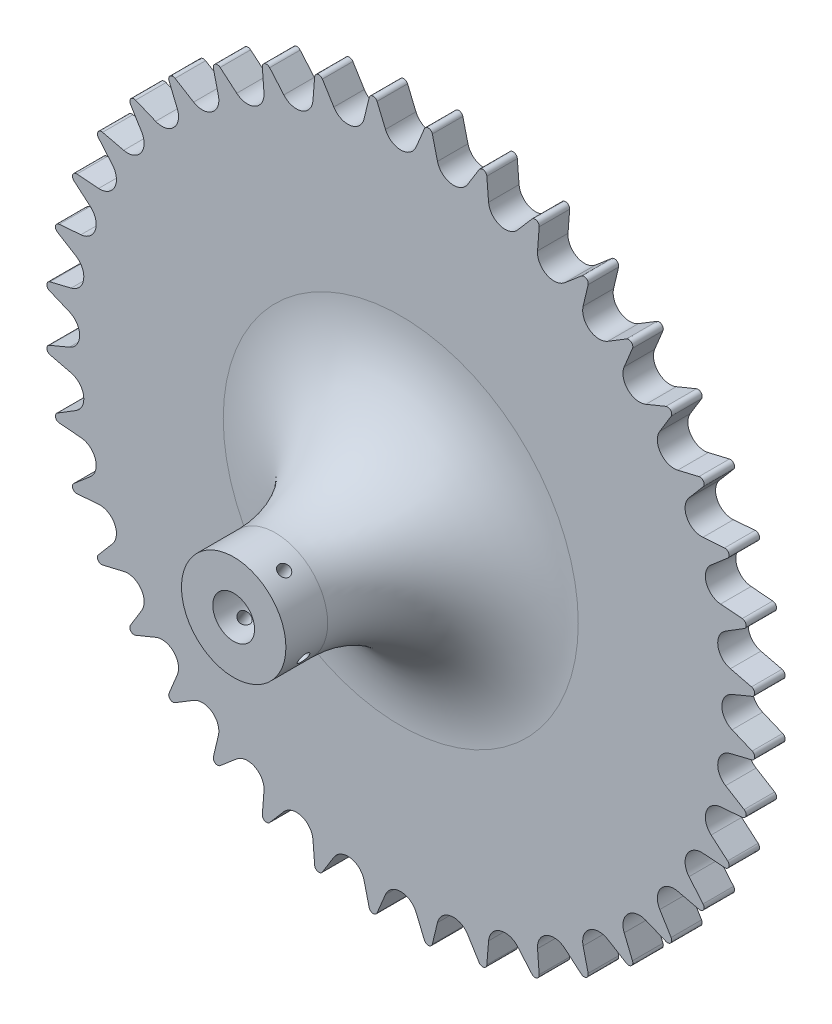
SolidWorks part; units mm, degrees
material "AISI 1010 Steel, hot rolled bar"
ref_plane "Front Plane" through (0, 0, 0) normal (0, 0, 1) x (1, 0, 0)
ref_plane "Top Plane" through (0, 0, 0) normal (0, 1, 0) x (1, 0, 0)
ref_plane "Right Plane" through (0, 0, 0) normal (1, 0, 0) x (0, 0, -1)
sketch "Sketch1" plane through (0, 0, 0) normal (0, 0, 1) x (1, 0, 0)
  line L0 (3.6626, 79.3215) -> (5.6677, 84.1262)
  line L1 (3.6626, 79.3215) -> (8.7911, 78.9179) construction
  line L2 (7.5623, 83.9771) -> (8.7911, 78.9179)
  line L3 (3.6626, 79.3215) -> (0, 0) construction
  line L4 (0, 0) -> (8.7911, 78.9179) construction
  line L5 (16.0261, 77.772) -> (18.7582, 82.2038)
  line L6 (20.6061, 81.7602) -> (21.0283, 76.5711)
  line L7 (27.995, 74.3074) -> (31.3867, 78.2573)
  line L8 (33.1425, 77.5301) -> (32.7478, 72.3388)
  line L9 (39.2746, 69.0132) -> (43.2424, 72.3839)
  line L10 (44.8629, 71.3909) -> (43.6609, 66.3253)
  line L11 (49.5871, 62.0196) -> (54.0334, 64.7281)
  line L12 (55.4785, 63.4939) -> (53.4989, 58.6786)
  line L13 (58.6786, 53.4989) -> (63.4939, 55.4785)
  line L14 (64.7281, 54.0334) -> (62.0196, 49.5871)
  line L15 (66.3253, 43.6609) -> (71.3909, 44.8629)
  line L16 (72.3839, 43.2424) -> (69.0132, 39.2746)
  line L17 (72.3388, 32.7478) -> (77.5301, 33.1425)
  line L18 (78.2573, 31.3867) -> (74.3074, 27.995)
  line L19 (76.5711, 21.0283) -> (81.7602, 20.6061)
  line L20 (82.2038, 18.7582) -> (77.772, 16.0261)
  line L21 (78.9179, 8.7911) -> (83.9771, 7.5623)
  line L22 (84.1262, 5.6677) -> (79.3215, 3.6626)
  line L23 (79.3215, -3.6626) -> (84.1262, -5.6677)
  line L24 (83.9771, -7.5623) -> (78.9179, -8.7911)
  line L25 (77.772, -16.0261) -> (82.2038, -18.7582)
  line L26 (81.7602, -20.6061) -> (76.5711, -21.0283)
  line L27 (74.3074, -27.995) -> (78.2573, -31.3867)
  line L28 (77.5301, -33.1425) -> (72.3388, -32.7478)
  line L29 (69.0132, -39.2746) -> (72.3839, -43.2424)
  line L30 (71.3909, -44.8629) -> (66.3253, -43.6609)
  line L31 (62.0196, -49.5871) -> (64.7281, -54.0334)
  line L32 (63.4939, -55.4785) -> (58.6786, -53.4989)
  line L33 (53.4989, -58.6786) -> (55.4785, -63.4939)
  line L34 (54.0334, -64.7281) -> (49.5871, -62.0196)
  line L35 (43.6609, -66.3253) -> (44.8629, -71.3909)
  line L36 (43.2424, -72.3839) -> (39.2746, -69.0132)
  line L37 (32.7478, -72.3388) -> (33.1425, -77.5301)
  line L38 (31.3867, -78.2573) -> (27.995, -74.3074)
  line L39 (21.0283, -76.5711) -> (20.6061, -81.7602)
  line L40 (18.7582, -82.2038) -> (16.0261, -77.772)
  line L41 (8.7911, -78.9179) -> (7.5623, -83.9771)
  line L42 (5.6677, -84.1262) -> (3.6626, -79.3215)
  line L43 (-3.6626, -79.3215) -> (-5.6677, -84.1262)
  line L44 (-7.5623, -83.9771) -> (-8.7911, -78.9179)
  line L45 (-16.0261, -77.772) -> (-18.7582, -82.2038)
  line L46 (-20.6061, -81.7602) -> (-21.0283, -76.5711)
  line L47 (-27.995, -74.3074) -> (-31.3867, -78.2573)
  line L48 (-33.1425, -77.5301) -> (-32.7478, -72.3388)
  line L49 (-39.2746, -69.0132) -> (-43.2424, -72.3839)
  line L50 (-44.8629, -71.3909) -> (-43.6609, -66.3253)
  line L51 (-49.5871, -62.0196) -> (-54.0334, -64.7281)
  line L52 (-55.4785, -63.4939) -> (-53.4989, -58.6786)
  line L53 (-58.6786, -53.4989) -> (-63.4939, -55.4785)
  line L54 (-64.7281, -54.0334) -> (-62.0196, -49.5871)
  line L55 (-66.3253, -43.6609) -> (-71.3909, -44.8629)
  line L56 (-72.3839, -43.2424) -> (-69.0132, -39.2746)
  line L57 (-72.3388, -32.7478) -> (-77.5301, -33.1425)
  line L58 (-78.2573, -31.3867) -> (-74.3074, -27.995)
  line L59 (-76.5711, -21.0283) -> (-81.7602, -20.6061)
  line L60 (-82.2038, -18.7582) -> (-77.772, -16.0261)
  line L61 (-78.9179, -8.7911) -> (-83.9771, -7.5623)
  line L62 (-84.1262, -5.6677) -> (-79.3215, -3.6626)
  line L63 (-79.3215, 3.6626) -> (-84.1262, 5.6677)
  line L64 (-83.9771, 7.5623) -> (-78.9179, 8.7911)
  line L65 (-77.772, 16.0261) -> (-82.2038, 18.7582)
  line L66 (-81.7602, 20.6061) -> (-76.5711, 21.0283)
  line L67 (-74.3074, 27.995) -> (-78.2573, 31.3867)
  line L68 (-77.5301, 33.1425) -> (-72.3388, 32.7478)
  line L69 (-69.0132, 39.2746) -> (-72.3839, 43.2424)
  line L70 (-71.3909, 44.8629) -> (-66.3253, 43.6609)
  line L71 (-62.0196, 49.5871) -> (-64.7281, 54.0334)
  line L72 (-63.4939, 55.4785) -> (-58.6786, 53.4989)
  line L73 (-53.4989, 58.6786) -> (-55.4785, 63.4939)
  line L74 (-54.0334, 64.7281) -> (-49.5871, 62.0196)
  line L75 (-43.6609, 66.3253) -> (-44.8629, 71.3909)
  line L76 (-43.2424, 72.3839) -> (-39.2746, 69.0132)
  line L77 (-32.7478, 72.3388) -> (-33.1425, 77.5301)
  line L78 (-31.3867, 78.2573) -> (-27.995, 74.3074)
  line L79 (-21.0283, 76.5711) -> (-20.6061, 81.7602)
  line L80 (-18.7582, 82.2038) -> (-16.0261, 77.772)
  line L81 (-8.7911, 78.9179) -> (-7.5623, 83.9771)
  line L82 (-5.6677, 84.1262) -> (-3.6626, 79.3215)
  line L83 (0, 80.85) -> (0, 0) construction
  line L84 (0, 0) -> (6.5906, 83.7411) construction
  circle A0 centre (0, 0) radius 80.85 construction
  arc A1 (-3.9676, 80.7526) -> (3.6626, 79.3215) centre (0, 80.85) ccw
  arc A2 (4.2537, 80.738) -> (8.4288, 80.4094) centre (0, 0) cw
  arc A3 (5.6677, 84.1262) -> (7.5623, 83.9771) centre (6.5906, 83.7411) cw
  arc A4 (8.7138, 80.3791) -> (16.0261, 77.772) centre (12.6477, 79.8546) ccw
  arc A5 (18.7582, 82.2038) -> (20.6061, 81.7602) centre (19.6094, 81.6791) cw
  arc A6 (21.1806, 78.0263) -> (27.995, 74.3074) centre (24.984, 76.8929) ccw
  arc A7 (31.3867, 78.2573) -> (33.1425, 77.5301) centre (32.1454, 77.6059) cw
  arc A8 (33.1258, 73.7523) -> (39.2746, 69.0132) centre (36.7051, 72.0379) ccw
  arc A9 (43.2424, 72.3839) -> (44.8629, 71.3909) centre (43.8899, 71.6218) cw
  arc A10 (44.2554, 67.6623) -> (49.5871, 62.0196) centre (47.5224, 65.409) ccw
  arc A11 (54.0334, 64.7281) -> (55.4785, 63.4939) centre (54.5536, 63.8741) cw
  arc A12 (54.2952, 59.9062) -> (58.6786, 53.4989) centre (57.1696, 57.1696) ccw
  arc A13 (63.4939, 55.4785) -> (64.7281, 54.0334) centre (63.8741, 54.5536) cw
  arc A14 (62.9981, 50.675) -> (66.3253, 43.6609) centre (65.409, 47.5224) ccw
  arc A15 (71.3909, 44.8629) -> (72.3839, 43.2424) centre (71.6218, 43.8899) cw
  arc A16 (70.1499, 40.196) -> (72.3388, 32.7478) centre (72.0379, 36.7051) ccw
  arc A17 (77.5301, 33.1425) -> (78.2573, 31.3867) centre (77.6059, 32.1454) cw
  arc A18 (75.5742, 28.7273) -> (76.5711, 21.0283) centre (76.8929, 24.984) ccw
  arc A19 (81.7602, 20.6061) -> (82.2038, 18.7582) centre (81.6791, 19.6094) cw
  arc A20 (79.1377, 16.5512) -> (78.9179, 8.7911) centre (79.8546, 12.6477) ccw
  arc A21 (83.9771, 7.5623) -> (84.1262, 5.6677) centre (83.7411, 6.5906) cw
  arc A22 (80.7526, 3.9676) -> (79.3215, -3.6626) centre (80.85, 0) ccw
  arc A23 (84.1262, -5.6677) -> (83.9771, -7.5623) centre (83.7411, -6.5906) cw
  arc A24 (80.3791, -8.7138) -> (77.772, -16.0261) centre (79.8546, -12.6477) ccw
  arc A25 (82.2038, -18.7582) -> (81.7602, -20.6061) centre (81.6791, -19.6094) cw
  arc A26 (78.0263, -21.1806) -> (74.3074, -27.995) centre (76.8929, -24.984) ccw
  arc A27 (78.2573, -31.3867) -> (77.5301, -33.1425) centre (77.6059, -32.1454) cw
  arc A28 (73.7523, -33.1258) -> (69.0132, -39.2746) centre (72.0379, -36.7051) ccw
  arc A29 (72.3839, -43.2424) -> (71.3909, -44.8629) centre (71.6218, -43.8899) cw
  arc A30 (67.6623, -44.2554) -> (62.0196, -49.5871) centre (65.409, -47.5224) ccw
  arc A31 (64.7281, -54.0334) -> (63.4939, -55.4785) centre (63.8741, -54.5536) cw
  arc A32 (59.9062, -54.2952) -> (53.4989, -58.6786) centre (57.1696, -57.1696) ccw
  arc A33 (55.4785, -63.4939) -> (54.0334, -64.7281) centre (54.5536, -63.8741) cw
  arc A34 (50.675, -62.9981) -> (43.6609, -66.3253) centre (47.5224, -65.409) ccw
  arc A35 (44.8629, -71.3909) -> (43.2424, -72.3839) centre (43.8899, -71.6218) cw
  arc A36 (40.196, -70.1499) -> (32.7478, -72.3388) centre (36.7051, -72.0379) ccw
  arc A37 (33.1425, -77.5301) -> (31.3867, -78.2573) centre (32.1454, -77.6059) cw
  arc A38 (28.7273, -75.5742) -> (21.0283, -76.5711) centre (24.984, -76.8929) ccw
  arc A39 (20.6061, -81.7602) -> (18.7582, -82.2038) centre (19.6094, -81.6791) cw
  arc A40 (16.5512, -79.1377) -> (8.7911, -78.9179) centre (12.6477, -79.8546) ccw
  arc A41 (7.5623, -83.9771) -> (5.6677, -84.1262) centre (6.5906, -83.7411) cw
  arc A42 (3.9676, -80.7526) -> (-3.6626, -79.3215) centre (0, -80.85) ccw
  arc A43 (-5.6677, -84.1262) -> (-7.5623, -83.9771) centre (-6.5906, -83.7411) cw
  arc A44 (-8.7138, -80.3791) -> (-16.0261, -77.772) centre (-12.6477, -79.8546) ccw
  arc A45 (-18.7582, -82.2038) -> (-20.6061, -81.7602) centre (-19.6094, -81.6791) cw
  arc A46 (-21.1806, -78.0263) -> (-27.995, -74.3074) centre (-24.984, -76.8929) ccw
  arc A47 (-31.3867, -78.2573) -> (-33.1425, -77.5301) centre (-32.1454, -77.6059) cw
  arc A48 (-33.1258, -73.7523) -> (-39.2746, -69.0132) centre (-36.7051, -72.0379) ccw
  arc A49 (-43.2424, -72.3839) -> (-44.8629, -71.3909) centre (-43.8899, -71.6218) cw
  arc A50 (-44.2554, -67.6623) -> (-49.5871, -62.0196) centre (-47.5224, -65.409) ccw
  arc A51 (-54.0334, -64.7281) -> (-55.4785, -63.4939) centre (-54.5536, -63.8741) cw
  arc A52 (-54.2952, -59.9062) -> (-58.6786, -53.4989) centre (-57.1696, -57.1696) ccw
  arc A53 (-63.4939, -55.4785) -> (-64.7281, -54.0334) centre (-63.8741, -54.5536) cw
  arc A54 (-62.9981, -50.675) -> (-66.3253, -43.6609) centre (-65.409, -47.5224) ccw
  arc A55 (-71.3909, -44.8629) -> (-72.3839, -43.2424) centre (-71.6218, -43.8899) cw
  arc A56 (-70.1499, -40.196) -> (-72.3388, -32.7478) centre (-72.0379, -36.7051) ccw
  arc A57 (-77.5301, -33.1425) -> (-78.2573, -31.3867) centre (-77.6059, -32.1454) cw
  arc A58 (-75.5742, -28.7273) -> (-76.5711, -21.0283) centre (-76.8929, -24.984) ccw
  arc A59 (-81.7602, -20.6061) -> (-82.2038, -18.7582) centre (-81.6791, -19.6094) cw
  arc A60 (-79.1377, -16.5512) -> (-78.9179, -8.7911) centre (-79.8546, -12.6477) ccw
  arc A61 (-83.9771, -7.5623) -> (-84.1262, -5.6677) centre (-83.7411, -6.5906) cw
  arc A62 (-80.7526, -3.9676) -> (-79.3215, 3.6626) centre (-80.85, 0) ccw
  arc A63 (-84.1262, 5.6677) -> (-83.9771, 7.5623) centre (-83.7411, 6.5906) cw
  arc A64 (-80.3791, 8.7138) -> (-77.772, 16.0261) centre (-79.8546, 12.6477) ccw
  arc A65 (-82.2038, 18.7582) -> (-81.7602, 20.6061) centre (-81.6791, 19.6094) cw
  arc A66 (-78.0263, 21.1806) -> (-74.3074, 27.995) centre (-76.8929, 24.984) ccw
  arc A67 (-78.2573, 31.3867) -> (-77.5301, 33.1425) centre (-77.6059, 32.1454) cw
  arc A68 (-73.7523, 33.1258) -> (-69.0132, 39.2746) centre (-72.0379, 36.7051) ccw
  arc A69 (-72.3839, 43.2424) -> (-71.3909, 44.8629) centre (-71.6218, 43.8899) cw
  arc A70 (-67.6623, 44.2554) -> (-62.0196, 49.5871) centre (-65.409, 47.5224) ccw
  arc A71 (-64.7281, 54.0334) -> (-63.4939, 55.4785) centre (-63.8741, 54.5536) cw
  arc A72 (-59.9062, 54.2952) -> (-53.4989, 58.6786) centre (-57.1696, 57.1696) ccw
  arc A73 (-55.4785, 63.4939) -> (-54.0334, 64.7281) centre (-54.5536, 63.8741) cw
  arc A74 (-50.675, 62.9981) -> (-43.6609, 66.3253) centre (-47.5224, 65.409) ccw
  arc A75 (-44.8629, 71.3909) -> (-43.2424, 72.3839) centre (-43.8899, 71.6218) cw
  arc A76 (-40.196, 70.1499) -> (-32.7478, 72.3388) centre (-36.7051, 72.0379) ccw
  arc A77 (-33.1425, 77.5301) -> (-31.3867, 78.2573) centre (-32.1454, 77.6059) cw
  arc A78 (-28.7273, 75.5742) -> (-21.0283, 76.5711) centre (-24.984, 76.8929) ccw
  arc A79 (-20.6061, 81.7602) -> (-18.7582, 82.2038) centre (-19.6094, 81.6791) cw
  arc A80 (-16.5512, 79.1377) -> (-8.7911, 78.9179) centre (-12.6477, 79.8546) ccw
  arc A81 (-7.5623, 83.9771) -> (-5.6677, 84.1262) centre (-6.5906, 83.7411) cw
  point P289 (0, 0)
  dimension "D1" = 161.7
  dimension "D2" = 3.9688
  dimension "D5" = 1
  dimension "D6" = 84
  dimension "D3" = 4.5
  dimension "D4" = 40
extrude "Boss-Extrude1" add sketch "Sketch1" along normal blind 7.3 contours A81 L81 A80 L80 A79 L79 A78 L78 A77 L77 A76 L76 A75 L75 A74 L74 A73 L73 A72 L72 A71 L71 A70 L70 A69 L69 A68 L68 A67 L67 A66 L66 A65 L65 A64 L64 A63 L63 A62 L62 A61 L61 A60 L60 A59 L59 A58 L58 A57 L57 A56 | A3 L0 A2 L2
sketch "Sketch2" plane through (0, 0, 7.3) normal (0, 0, 1) x (1, 0, 0)
  circle A0 centre (0, 0) radius 12.5
  dimension "D1" = 25
extrude "Boss-Extrude2" add sketch "Sketch2" along normal blind 40
fillet "Fillet1" radius 30 1 edges at (12.5, 0, 7.3)
sketch "Sketch3" plane through (0, 0, 47.3) normal (0, 0, 1) x (1, 0, 0)
  circle A0 centre (0, 0) radius 5
  dimension "D1" = 10
extrude "Cut-Extrude1" cut sketch "Sketch3" against normal through all
hole_wizard "Ø1.0mm Dowel Hole1" positions "3DSketch1" profile "Sketch4" hole size "Ø1.0" standard "ANSI Metric"
sketch3d "3DSketch1"
  point P0 (-6.8176, -10.4771, 42.0201)
  point P2 (-11.0684, 5.8086, 41.6583)
sketch "Sketch4" plane through (-6.8176, -10.4771, 42.0201) normal (0, 0, 1) x (0.8382, -0.5454, 0)
  line L0 (0, 0) -> (0, 34)
  line L1 (0, 34) -> (1.4, 33.1588)
  line L2 (1.4, 33.1588) -> (1.4, 0)
  line L5 (1.4, 0) -> (0, 0)
  line L10 (0, 34) -> (-1.4, 33.1588) construction
  line L11 (0, -6.35) -> (0, 107.95) construction
  dimension "Hole Dia." = 2.8
  dimension "Hole Depth" = 34
  dimension "Drill Angle" = 118
sketch "Sketch5" plane through (0, 0, 0) normal (0, 0, -1) x (-1, 0, 0)
  line L0 (-0.9617, 76.9995) -> (2.0291, 76.7641)
  line L1 (-0.9617, 76.9995) -> (-0.3094, 85.2872)
  line L2 (12.9952, 75.9011) -> (13.6474, 84.1888)
  line L3 (-0.3094, 85.2872) -> (13.6474, 84.1888)
  line L4 (10.0044, 76.1365) -> (12.9952, 75.9011)
  arc A0 (2.0291, 76.7641) -> (10.0044, 76.1365) centre (6.3676, 80.9087) ccw
  arc A2 (7.5623, 83.9771) -> (5.6677, 84.1262) centre (6.5906, 83.7411) ccw construction
  arc A3 (-3.6626, 79.3215) -> (3.6626, 79.3215) centre (0, 80.85) ccw construction
  arc A4 (8.7911, 78.9179) -> (16.0261, 77.772) centre (12.6477, 79.8546) ccw construction
  point P17 (6.669, 84.738)
  dimension "D2" = 3
  dimension "D3" = 3
  dimension "D4" = 6
  dimension "D1" = 14
extrude "Cut-Extrude2" [suppressed] cut sketch "Sketch5" against normal blind 10
pattern_circular "CirPattern1" [suppressed] count 20 over 360
sketch "Sketch6" plane through (0, 0, 0) normal (0, 1, 0) x (1, 0, 0)
  line L0 (-84.7411, -7.3) -> (-83.9771, -7.3) construction
  line L1 (-84.3591, -7.3) -> (85.648, -7.3)
  line L2 (-84.3591, -7.3) -> (-84.3591, -52.0573)
  line L3 (-84.3591, -52.0573) -> (85.648, -52.0573)
  line L4 (85.648, -7.3) -> (85.648, -52.0573)
extrude "Cut-Extrude3" [suppressed] cut sketch "Sketch6" against normal through all both and the other way through all
sketch "Sketch7" plane through (0, 0, 0) normal (0, 0, -1) x (-1, 0, 0)
  line L1 (12.6, -7.2746) -> (12.6, 7.2746)
  line L2 (12.6, 7.2746) -> (0, 14.5492)
  line L3 (0, 14.5492) -> (-12.6, 7.2746)
  line L4 (-12.6, 7.2746) -> (-12.6, -7.2746)
  line L5 (-12.6, -7.2746) -> (0, -14.5492)
  line L6 (0, -14.5492) -> (12.6, -7.2746)
  circle A0 centre (0, 0) radius 12.6 construction
  dimension "D1" = 25.2
extrude "Cut-Extrude4" [suppressed] cut sketch "Sketch7" against normal through all both
